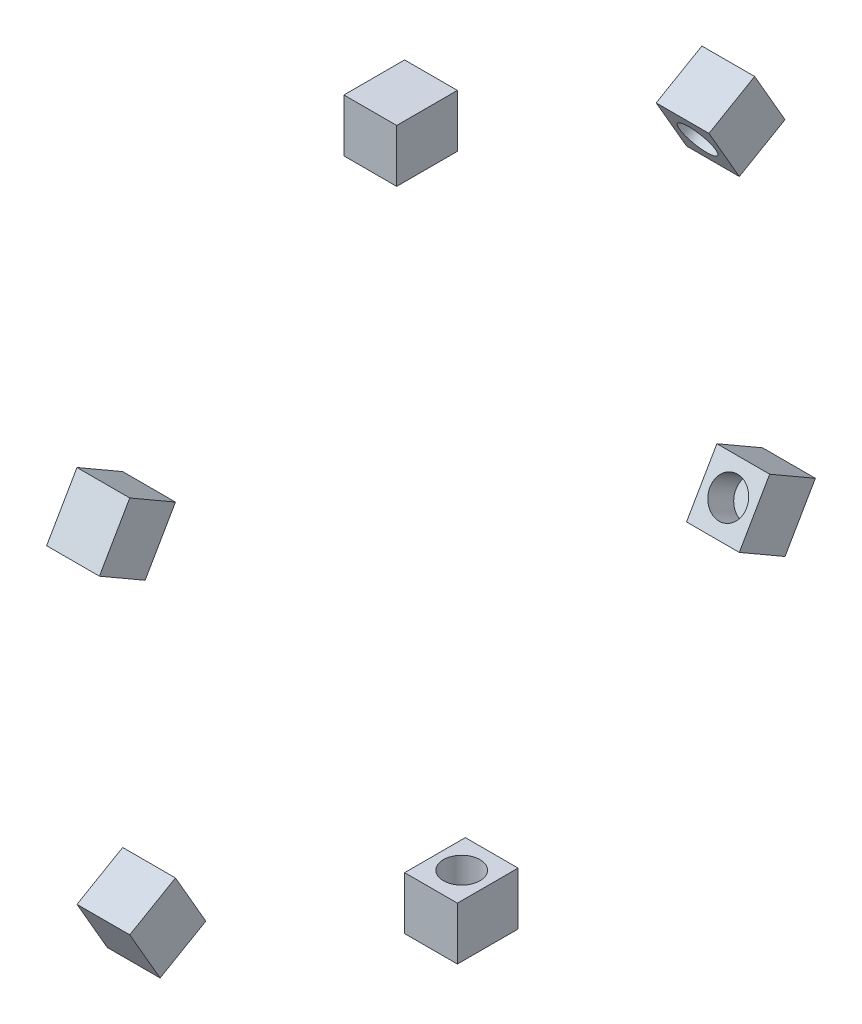
SolidWorks part; units mm, degrees
ref_plane "Front Plane" through (0, 0, 0) normal (0, 0, 1) x (1, 0, 0)
ref_plane "Top Plane" through (0, 0, 0) normal (0, 1, 0) x (1, 0, 0)
ref_plane "Right Plane" through (0, 0, 0) normal (1, 0, 0) x (0, 0, -1)
sketch "Sketch1" plane through (0, 0, 0) normal (0, 0, 1) x (1, 0, 0)
  line L2 (-2336.4077, -1721.4292) -> (2327.9252, -1721.4292)
  line L3 (-2336.4077, -1721.4292) -> (-2336.4077, -2121.4292)
  line L4 (-2336.4077, -2121.4292) -> (2327.9252, -2121.4292)
  line L5 (2327.9252, -1721.4292) -> (2327.9252, -2121.4292)
  line L6 (-2336.4077, -1721.4292) -> (2327.9252, -2121.4292) construction
  line L7 (-2336.4077, -2121.4292) -> (2327.9252, -1721.4292) construction
  point P2 (-4.2413, -1921.4292)
  dimension "D1" = 400
  dimension "D2" = 4664.3329
sketch "Sketch2" plane through (0, 0, 0) normal (0, 0, 1) x (1, 0, 0)
  line L0 (-2336.4077, -1721.4292) -> (2327.9252, -1721.4292) construction
  line L1 (-34.2413, -1691.4292) -> (25.7587, -1691.4292)
  line L2 (-34.2413, -1691.4292) -> (-34.2413, -1751.4292)
  line L3 (-34.2413, -1751.4292) -> (25.7587, -1751.4292)
  line L4 (25.7587, -1691.4292) -> (25.7587, -1751.4292)
  line L5 (-34.2413, -1691.4292) -> (25.7587, -1751.4292) construction
  line L6 (-34.2413, -1751.4292) -> (25.7587, -1691.4292) construction
  point P0 (-4.2413, -1721.4292)
  dimension "D1" = 60
  dimension "D2" = 60
extrude "Boss-Extrude1" add sketch "Sketch2" along normal blind 69
sketch "Sketch3" plane through (0, 0, 69) normal (0, 0, 1) x (1, 0, 0)
  line L0 (-2336.4077, -1721.4292) -> (2327.9252, -1721.4292) construction
  circle A0 centre (-4.2413, -1721.4292) radius 37.7303
sketch "Sketch4" plane through (0, -1751.4292, 0) normal (0, -1, 0) x (1, 0, 0)
  circle A0 centre (-4.2413, 34.8668) radius 20.7977
  point P2 (-4.2413, 36.5579)
  point P3 (0, 0)
  point P4 (-2.9428, 25.5654)
  point P5 (-4.2413, 34.8668)
extrude "Cut-Extrude2" cut sketch "Sketch4" against normal blind 34
sketch "Sketch5" plane through (0, 0, 0) normal (0, 0, 1) x (1, 0, 0)
  circle A0 centre (0, 0) radius 408.6542
pattern_circular "CirPattern1" count 6 every 60 about axis through (0, -2121.4292, 0) along (1, 0, 0) of bodies 103
